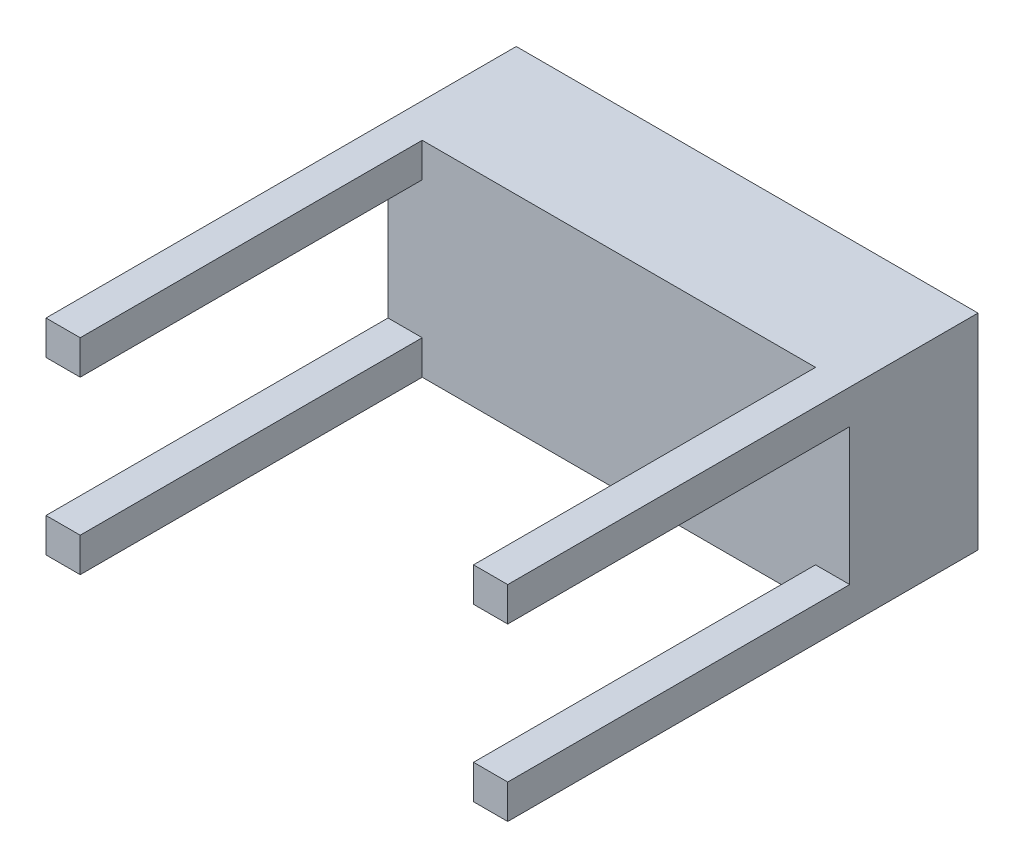
SolidWorks part; units mm, degrees
ref_plane "Plano frontal" through (0, 0, 0) normal (0, 0, 1) x (1, 0, 0)
ref_plane "Plano superior" through (0, 0, 0) normal (0, 1, 0) x (1, 0, 0)
ref_plane "Plano direito" through (0, 0, 0) normal (1, 0, 0) x (0, 0, -1)
sketch "Esboço1" plane through (0, 0, 0) normal (0, 0, 1) x (1, 0, 0)
  line L1 (0, 0) -> (-540, 0)
  line L2 (0, 0) -> (0, 240)
  line L3 (0, 240) -> (-540, 240)
  line L4 (-540, 0) -> (-540, 240)
  dimension "D1" = 540
  dimension "D2" = 240
extrude "Ressalto-extrusão1" add sketch "Esboço1" along normal blind 150
sketch "Esboço2" plane through (0, 0, 150) normal (0, 0, 1) x (1, 0, 0)
  line L0 (-270, 240) -> (-270, 0) construction
  line L1 (-540, 240) -> (-500, 240)
  line L2 (-540, 240) -> (-540, 200)
  line L3 (-540, 200) -> (-500, 200)
  line L4 (-500, 240) -> (-500, 200)
  line L5 (-540, 0) -> (-500, 0)
  line L6 (-540, 0) -> (-540, 40)
  line L7 (-540, 40) -> (-500, 40)
  line L8 (-500, 0) -> (-500, 40)
  line L9 (0, 240) -> (-540, 240) construction
  line L10 (-540, 0) -> (0, 0) construction
  line L11 (-40, 0) -> (-40, 40)
  line L12 (0, 40) -> (-40, 40)
  line L13 (0, 0) -> (0, 40)
  line L14 (0, 0) -> (-40, 0)
  line L15 (-40, 240) -> (-40, 200)
  line L16 (0, 200) -> (-40, 200)
  line L17 (0, 240) -> (0, 200)
  line L18 (0, 240) -> (-40, 240)
  dimension "D1" = 40
extrude "Ressalto-extrusão2" add sketch "Esboço2" along normal blind 400
